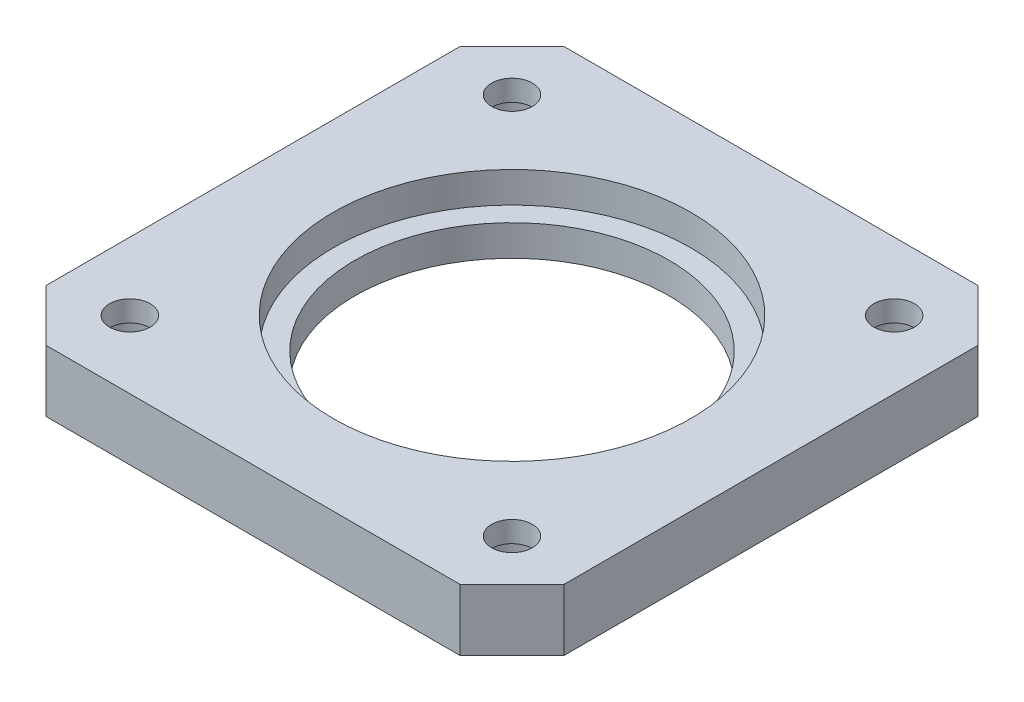
SolidWorks part; units mm, degrees
ref_plane "前视基准面" through (0, 0, 0) normal (0, 0, 1) x (1, 0, 0)
ref_plane "上视基准面" through (0, 0, 0) normal (0, 1, 0) x (1, 0, 0)
ref_plane "右视基准面" through (0, 0, 0) normal (1, 0, 0) x (0, 0, -1)
other "Configuration Table"
sketch "草图1" plane through (0, 0, 0) normal (0, 1, 0) x (1, 0, 0)
  line L0 (5.5, 5.5) -> (36.5, 5.5) construction
  line L1 (0, 0) -> (42, 0)
  line L2 (0, 0) -> (0, 42)
  line L3 (0, 42) -> (42, 42)
  line L4 (42, 0) -> (42, 42)
  line L5 (5.5, 5.5) -> (5.5, 36.5) construction
  line L6 (0, 21) -> (42, 21) construction
  circle A0 centre (5.5, 5.5) radius 1.65
  circle A1 centre (36.5, 5.5) radius 1.65
  circle A2 centre (36.5, 36.5) radius 1.65
  circle A3 centre (5.5, 36.5) radius 1.65
  circle A4 centre (21, 21) radius 12.75
  dimension "D3" = 3.3
  dimension "D9" = 5.5
  dimension "D10" = 5.5
  dimension "D11" = 25.5
  dimension "D1" = 42
  dimension "D2" = 42
  dimension "D6" = 90
  dimension "D7" = 31
  dimension "D8" = 31
  dimension "D4" = 2
  dimension "D5" = 2
extrude "凸台-拉伸1" add sketch "草图1" along normal blind 5
sketch "草图2" plane through (0, 5, 0) normal (0, 1, 0) x (1, 0, 0)
  circle A0 centre (21, 21) radius 14.5
  dimension "D1" = 29
extrude "切除-拉伸1" cut sketch "草图2" against normal blind 2.5
chamfer "倒角1" distance 4.2 angle 45 4 edges at (42, 2.5, -42) (0, 2.5, -42) (0, 2.5, 0) (42, 2.5, 0)
sketch "草图3" plane through (0, 0, 0) normal (0, -1, 0) x (1, 0, 0)
  line L0 (0, -21) -> (42, -21) construction
  line L1 (0, -37.8) -> (0, -4.2) construction
  line L2 (42, -4.2) -> (42, -37.8) construction
  circle A0 centre (38, -21) radius 1.95
  circle A1 centre (21, -38) radius 1.95
  circle A2 centre (4, -21) radius 1.95
  circle A3 centre (21, -4) radius 1.95
  point P8 (23.254, -3.7714)
  point P9 (21, -21)
  point P10 (21, -21)
  point P11 (21, -4)
  point P18 (21, -21)
  dimension "D1" = 4
  dimension "D3" = 3.9
  dimension "D2" = 4
extrude "切除-拉伸2" cut sketch "草图3" against normal blind 3.2
chamfer "倒角2" distance 0.5 angle 45 4 edges at (21, 0, -39.95) (4, 0, -22.95) (38, 0, -22.95) (21, 0, -5.95)
sketch "草图4" plane through (0, 0, 0) normal (0, -1, 0) x (1, 0, 0)
  circle A0 centre (5.5, -5.5) radius 3
  circle A1 centre (36.5, -5.5) radius 3
  circle A2 centre (36.5, -36.5) radius 3
  circle A3 centre (5.5, -36.5) radius 3
  dimension "D1" = 6
extrude "切除-拉伸3" cut sketch "草图4" against normal blind 3.3
